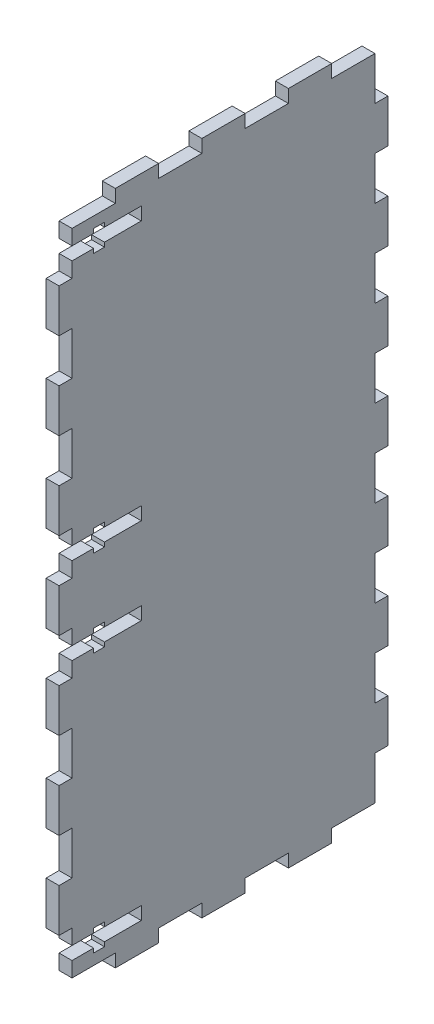
SolidWorks part; units mm, degrees
ref_plane "Front Plane" through (0, 0, 0) normal (0, 0, 1) x (1, 0, 0)
ref_plane "Top Plane" through (0, 0, 0) normal (0, 1, 0) x (1, 0, 0)
ref_plane "Right Plane" through (0, 0, 0) normal (1, 0, 0) x (0, 0, -1)
sketch "Sketch1" plane through (0, 0, 0) normal (1, 0, 0) x (0, 0, -1)
  line L1 (10, 153.0059) -> (20, 153.0059)
  line L2 (0, 140) -> (0, 143.5)
  line L3 (0, 150.0059) -> (10, 150.0059)
  line L4 (10, 150.0059) -> (10, 153.0059)
  line L5 (-3, 120) -> (0, 120)
  line L6 (-3, 130) -> (-3, 140)
  line L7 (0, 130) -> (-3, 130)
  line L8 (0, 120) -> (0, 130)
  line L9 (-3, 100) -> (0, 100)
  line L10 (-3, 110) -> (-3, 120)
  line L11 (0, 110) -> (-3, 110)
  line L12 (-3, 140) -> (0, 140)
  line L13 (0, 100) -> (0, 110)
  line L14 (-3, 80) -> (0, 80)
  line L15 (-3, 90) -> (-3, 100)
  line L16 (0, 90) -> (-3, 90)
  line L17 (0, 80) -> (0, 83.5)
  line L18 (-3, 60) -> (0, 60)
  line L19 (-3, 70) -> (-3, 80)
  line L20 (0, 70) -> (-3, 70)
  line L21 (0, 60) -> (0, 63.5)
  line L22 (-3, 40) -> (0, 40)
  line L23 (-3, 50) -> (-3, 60)
  line L24 (0, 50) -> (-3, 50)
  line L25 (0, 40) -> (0, 50)
  line L26 (-3, 20) -> (0, 20)
  line L27 (-3, 30) -> (-3, 40)
  line L28 (0, 30) -> (-3, 30)
  line L29 (0, 20) -> (0, 30)
  line L30 (-3, 10) -> (-3, 20)
  line L31 (20, 153.0059) -> (20, 150.0059)
  line L32 (0, 10) -> (-3, 10)
  line L33 (0, 0) -> (0, 3.5)
  line L34 (20, 150.0059) -> (30, 150.0059)
  line L35 (30, 153.0059) -> (40, 153.0059)
  line L36 (30, 150.0059) -> (30, 153.0059)
  line L37 (40, 153.0059) -> (40, 150.0059)
  line L38 (40, 150.0059) -> (50, 150.0059)
  line L39 (50, 153.0059) -> (60, 153.0059)
  line L40 (50, 150.0059) -> (50, 153.0059)
  line L41 (60, 153.0059) -> (60, 150.0059)
  line L42 (60, 150.0059) -> (70, 150.0059)
  line L46 (0, 10) -> (0, 6.5)
  line L47 (7.5, 6.5) -> (16, 6.5)
  line L48 (16, 3.5) -> (7.5, 3.5)
  line L49 (70, 0) -> (70, 3.5)
  line L50 (70, 10) -> (73, 10)
  line L51 (73, 10) -> (73, 20)
  line L52 (70, 20) -> (70, 30)
  line L53 (70, 30) -> (73, 30)
  line L54 (73, 30) -> (73, 40)
  line L55 (73, 20) -> (70, 20)
  line L56 (70, 40) -> (70, 50)
  line L57 (70, 50) -> (73, 50)
  line L58 (73, 50) -> (73, 60)
  line L59 (73, 40) -> (70, 40)
  line L60 (70, 60) -> (70, 63.5)
  line L61 (70, 70) -> (73, 70)
  line L62 (73, 70) -> (73, 80)
  line L63 (73, 60) -> (70, 60)
  line L64 (70, 80) -> (70, 83.5)
  line L65 (70, 90) -> (73, 90)
  line L66 (73, 90) -> (73, 100)
  line L67 (73, 80) -> (70, 80)
  line L68 (70, 100) -> (70, 110)
  line L69 (73, 140) -> (70, 140)
  line L70 (70, 110) -> (73, 110)
  line L71 (73, 110) -> (73, 120)
  line L72 (73, 100) -> (70, 100)
  line L73 (70, 120) -> (70, 130)
  line L74 (70, 130) -> (73, 130)
  line L75 (73, 130) -> (73, 140)
  line L76 (73, 120) -> (70, 120)
  line L77 (70, 140) -> (70, 143.5)
  line L78 (7.5, 2.5) -> (5, 2.5)
  line L79 (0, 6.5) -> (5, 6.5)
  line L80 (60, 0) -> (70, 0)
  line L81 (60, -3) -> (60, 0)
  line L82 (50, 0) -> (50, -3)
  line L83 (50, -3) -> (60, -3)
  line L84 (40, 0) -> (50, 0)
  line L85 (40, -3) -> (40, 0)
  line L86 (30, 0) -> (30, -3)
  line L87 (30, -3) -> (40, -3)
  line L88 (20, 0) -> (30, 0)
  line L89 (20, -3) -> (20, 0)
  line L90 (10, 0) -> (10, -3)
  line L91 (0, 0) -> (10, 0)
  line L92 (10, -3) -> (20, -3)
  line L93 (16, 6.5) -> (16, 3.5)
  line L94 (7.5, 2.5) -> (7.5, 3.5)
  line L95 (7.5, 7.5) -> (5, 7.5)
  line L96 (5, 2.5) -> (5, 3.5)
  line L97 (5, 6.5) -> (5, 7.5)
  line L98 (7.5, 6.5) -> (7.5, 7.5)
  line L99 (5, 3.5) -> (0, 3.5)
  line L100 (5, 63.5) -> (0, 63.5)
  line L101 (0, 66.5) -> (5, 66.5)
  line L102 (7.5, 66.5) -> (16, 66.5)
  line L103 (16, 63.5) -> (7.5, 63.5)
  line L104 (7.5, 62.5) -> (5, 62.5)
  line L105 (16, 66.5) -> (16, 63.5)
  line L106 (7.5, 62.5) -> (7.5, 63.5)
  line L107 (7.5, 67.5) -> (5, 67.5)
  line L108 (5, 62.5) -> (5, 63.5)
  line L109 (5, 66.5) -> (5, 67.5)
  line L110 (7.5, 66.5) -> (7.5, 67.5)
  line L111 (5, 83.5) -> (0, 83.5)
  line L112 (0, 86.5) -> (5, 86.5)
  line L113 (7.5, 86.5) -> (16, 86.5)
  line L114 (16, 83.5) -> (7.5, 83.5)
  line L115 (7.5, 82.5) -> (5, 82.5)
  line L116 (16, 86.5) -> (16, 83.5)
  line L117 (7.5, 82.5) -> (7.5, 83.5)
  line L118 (7.5, 87.5) -> (5, 87.5)
  line L119 (5, 82.5) -> (5, 83.5)
  line L120 (5, 86.5) -> (5, 87.5)
  line L121 (7.5, 86.5) -> (7.5, 87.5)
  line L122 (7.5, 146.5) -> (16, 146.5)
  line L123 (16, 143.5) -> (7.5, 143.5)
  line L124 (7.5, 142.5) -> (5, 142.5)
  line L125 (16, 146.5) -> (16, 143.5)
  line L126 (7.5, 142.5) -> (7.5, 143.5)
  line L127 (7.5, 147.5) -> (5, 147.5)
  line L128 (5, 142.5) -> (5, 143.5)
  line L129 (5, 146.5) -> (5, 147.5)
  line L130 (7.5, 146.5) -> (7.5, 147.5)
  line L131 (5, 143.5) -> (0, 143.5)
  line L132 (0, 146.5) -> (5, 146.5)
  line L133 (0, 0) -> (70, 0) construction
  line L134 (70, 6.5) -> (70, 10)
  line L135 (70, 3.5) -> (70, 6.5)
  line L136 (70, 63.5) -> (70, 66.5)
  line L137 (70, 83.5) -> (70, 90)
  line L139 (70, 143.5) -> (70, 146.5)
  line L179 (70, 66.5) -> (70, 70)
  line L181 (70, 146.5) -> (70, 150.0059)
  line L182 (0, 146.5) -> (0, 150.0059)
  line L183 (0, 86.5) -> (0, 90)
  line L184 (0, 66.5) -> (0, 70)
  point P49 (8, 5)
  point P94 (8, 5)
  point P99 (8, 65)
  point P109 (8, 65)
  point P118 (8, 85)
  point P123 (8, 85)
  point P133 (8, 145)
  point P138 (8, 145)
  dimension "D1" = 2
  dimension "D2" = 2
  dimension "D3" = 2
extrude "Boss-Extrude1" add sketch "Sketch1" along normal blind 3
